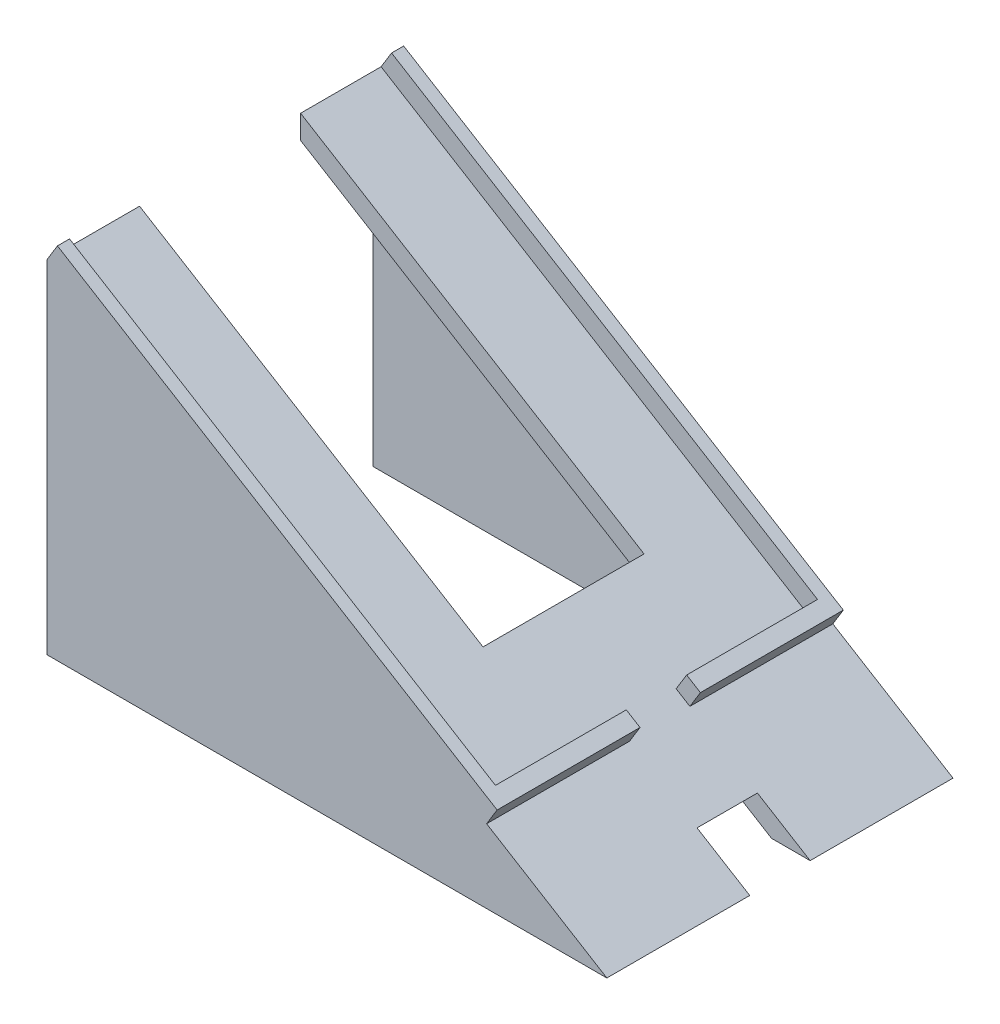
SolidWorks part; units mm, degrees
ref_plane "Front Plane" through (0, 0, 0) normal (0, 0, 1) x (1, 0, 0)
ref_plane "Top Plane" through (0, 0, 0) normal (0, 1, 0) x (1, 0, 0)
ref_plane "Right Plane" through (0, 0, 0) normal (1, 0, 0) x (0, 0, -1)
sketch "Sketch1" plane through (0, 0, 0) normal (0, 0, 1) x (1, 0, 0)
  line L0 (0, 0) -> (0, 5)
  line L1 (0, 95) -> (139.0827, 10)
  line L2 (139.0827, 10) -> (139.0827, 0)
  line L3 (139.0827, 0) -> (0, 0)
  line L4 (5, 5) -> (5, 86.0844)
  line L5 (5, 86.0844) -> (134.0827, 7.1959)
  line L6 (134.0827, 7.1959) -> (134.0827, 5)
  line L7 (134.0827, 5) -> (5, 5)
  line L8 (5, 86.0844) -> (0, 89.1402)
  line L9 (5, 5) -> (0, 5)
  line L10 (0, 89.1402) -> (0, 95)
  line L12 (0, 0) -> (0, 95) construction
  dimension "D1" = 163
  dimension "D2" = 10
  dimension "D3" = 95
  dimension "D4" = 5
extrude "Boss-Extrude2" add sketch "Sketch1" along normal blind 86 contours L10 L8 L5 L6 L7 L9 L0 L3 L2 L1
sketch "Sketch2" plane through (0, 0, 86) normal (0, 0, 1) x (1, 0, 0)
  line L0 (0, 89.1402) -> (134.0827, 7.1959)
  line L1 (134.0827, 7.1959) -> (134.0827, 5)
  line L2 (134.0827, 5) -> (0, 5)
  line L3 (0, 5) -> (0, 89.1402)
extrude "Boss-Extrude3" add sketch "Sketch2" against normal blind 5
sketch "Sketch3" plane through (42.2708, 69.1663, 0) normal (0.5215, 0.8533, 0) x (0, 0, -1)
  line L0 (0, 49.5399) -> (0, -78.4601)
  line L2 (-86, -78.4601) -> (-86, 49.5399)
  line L3 (-86, 49.5399) -> (-83, 49.5399)
  line L4 (-86, 49.5399) -> (0, 49.5399) construction
  line L5 (-83, 49.5399) -> (-83, -74.4601)
  line L7 (-3, -74.4601) -> (-3, 49.5399)
  line L8 (-3, 49.5399) -> (0, 49.5399)
  line L9 (-86, -78.4601) -> (0, -78.4601)
  line L10 (-83, -74.4601) -> (-3, -74.4601)
  line L11 (-86, -113.4601) -> (0, -113.4601) construction
  dimension "D1" = 3
  dimension "D2" = 3
  dimension "D3" = 4
  dimension "D4" = 35
extrude "Boss-Extrude4" add sketch "Sketch3" along normal blind 5
sketch "Sketch5" plane through (42.2708, 69.1663, 0) normal (0.5215, 0.8533, 0) x (0, 0, -1)
  line L0 (-43, 49.5399) -> (-23, 49.5399)
  line L1 (-83, 49.5399) -> (-3, 49.5399) construction
  line L2 (-23, 49.5399) -> (-23, -50.4601)
  line L3 (-23, -50.4601) -> (-63, -50.4601)
  line L4 (-63, -50.4601) -> (-63, 49.5399)
  line L5 (-63, 49.5399) -> (-43, 49.5399)
  dimension "D1" = 20
  dimension "D2" = 20
  dimension "D3" = 100
extrude "Cut-Extrude2" cut sketch "Sketch5" against normal through all
sketch "Sketch6" plane through (0, 0, 0) normal (0, 0, -1) x (-1, 0, 0)
  line L0 (0, 89.1402) -> (-134.0827, 7.1959)
  line L1 (-134.0827, 7.1959) -> (-134.0827, 5)
  line L2 (-134.0827, 5) -> (0, 5)
  line L3 (0, 5) -> (0, 89.1402)
extrude "Boss-Extrude5" add sketch "Sketch6" against normal blind 5
sketch "Sketch7" plane through (0, 5, 0) normal (0, 1, 0) x (1, 0, 0)
  line L0 (0, -5) -> (135.1931, -5)
  line L1 (135.1931, -5) -> (134.0827, -81)
  line L2 (134.0827, -81) -> (0, -81)
  line L3 (0, -81) -> (0, -63)
  line L4 (0, -63) -> (62.1932, -63)
  line L5 (62.1932, -63) -> (62.1932, -23)
  line L6 (62.1932, -23) -> (0, -23)
  line L7 (0, -23) -> (0, -5)
  line L8 (62.1932, -23) -> (62.1932, -63) construction
extrude "Cut-Extrude3" cut sketch "Sketch7" against normal through all
sketch "Sketch8" plane through (43.056, -26.3136, 0) normal (-0.8533, 0.5215, 0) x (0, 0, 1)
  line L1 (23, 36.6984) -> (63, 36.6984)
  line L2 (23, 36.6984) -> (23, 30.8386)
  line L3 (23, 30.8386) -> (63, 30.8386)
  line L4 (63, 36.6984) -> (63, 30.8386)
extrude "Cut-Extrude4" cut sketch "Sketch8" against normal through all
sketch "Sketch10" plane through (44.8782, 73.4327, 0) normal (0.5215, 0.8533, 0) x (0.8533, -0.5215, 0)
sketch "Sketch11" plane through (139.0827, 0, 0) normal (1, 0, 0) x (0, 0, -1)
  line L1 (-86, 10) -> (0, 10)
  line L2 (-86, 10) -> (-86, 0)
  line L3 (-86, 0) -> (0, 0)
  line L4 (0, 10) -> (0, 0)
extrude "Cut-Extrude6" cut sketch "Sketch11" against normal through all
ref_plane "Plane1" through (0, 0, 0) normal (-1, 0, 0) x (0, 0, 1)
sketch "Sketch13" plane through (0, 0, 0) normal (-1, 0, 0) x (0, 0, 1)
  line L0 (43, 10) -> (50.5, 10)
  line L1 (81, 10) -> (5, 10) construction
  line L2 (50.5, 10) -> (50.5, 18)
  line L3 (50.5, 18) -> (35.5, 18)
  line L4 (35.5, 18) -> (35.5, 10)
  line L5 (35.5, 10) -> (43, 10)
  dimension "D1" = 7.5
  dimension "D2" = 7.5
  dimension "D3" = 8
extrude "Cut-Extrude8" cut sketch "Sketch13" against normal through all
sketch "Sketch14" plane through (66.9475, -40.9148, 0) normal (0.8533, -0.5215, 0) x (0, 0, -1)
  line L0 (-35.5, 81.0605) -> (-35.5, 86.0605)
  line L1 (-86, 86.0605) -> (0, 86.0605) construction
  line L2 (-35.5, 86.0605) -> (-50.5, 86.0605)
  line L3 (-50.5, 86.0605) -> (-50.5, 81.0605)
  line L4 (-50.5, 81.0605) -> (-35.5, 81.0605)
extrude "Cut-Extrude9" cut sketch "Sketch14" against normal blind 10
